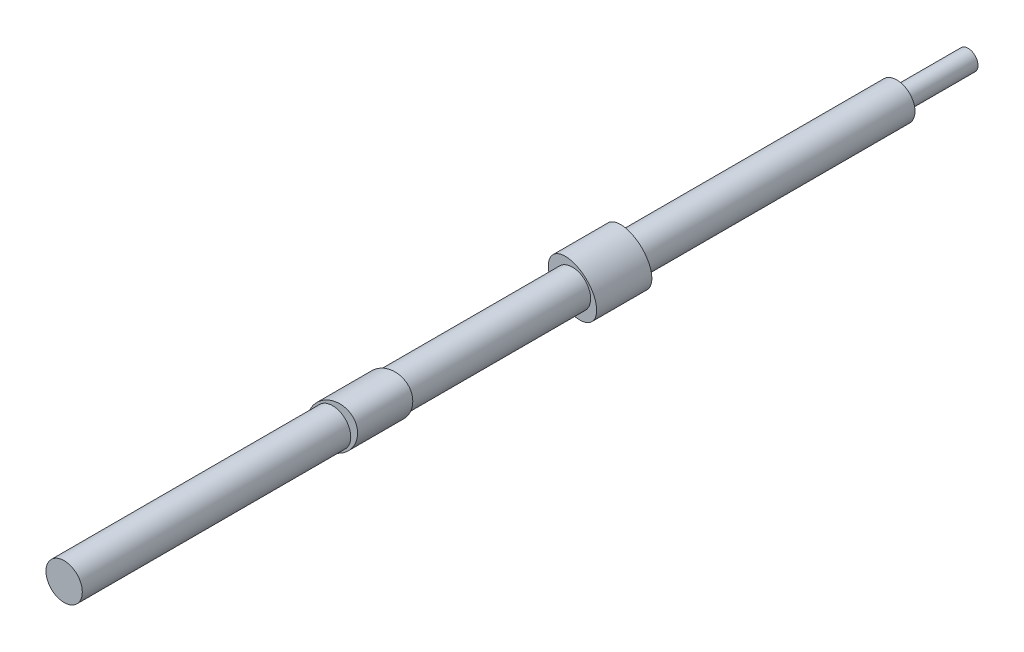
SolidWorks part; units mm, degrees
ref_plane "Ön Düzlem" through (0, 0, 0) normal (0, 0, 1) x (1, 0, 0)
ref_plane "Üst Düzlem" through (0, 0, 0) normal (0, 1, 0) x (1, 0, 0)
ref_plane "Sağ Düzlem" through (0, 0, 0) normal (1, 0, 0) x (0, 0, -1)
sketch "Çizim1" plane through (0, 0, 0) normal (0, 0, 1) x (1, 0, 0)
  circle A0 centre (0, 0) radius 3.9498
extrude "Yükseklik-Ekstrüzyon1" add sketch "Çizim1" along normal mid plane 181
ref_plane "Düzlem1" through (0, 0, 26.1437) normal (0, 0, 1) x (1, 0, 0)
ref_plane "Düzlem2" through (0, 0, -26) normal (0, 0, 1) x (1, 0, 0)
sketch "Çizim2" plane through (0, 0, 26.1437) normal (0, 0, 1) x (1, 0, 0)
  ellipse E0 centre (0, 0) end of major axis (4.6882, 3.7328) minor radius 4.4127
extrude "Yükseklik-Ekstrüzyon2" add sketch "Çizim2" along normal mid plane 12
sketch "Çizim3" plane through (0, 0, -26) normal (0, 0, 1) x (1, 0, 0)
  ellipse E0 centre (0, 0) end of major axis (-4.2597, 4.1653) minor radius 4.3916
extrude "Yükseklik-Ekstrüzyon3" add sketch "Çizim3" along normal mid plane 12
sketch "Çizim4" plane through (0, 0, 90.5) normal (0, 0, 1) x (1, 0, 0)
  circle A0 centre (0, 0) radius 1.0446
sketch "Çizim5" plane through (0, 0, -90.5) normal (0, 0, -1) x (-1, 0, 0)
  circle A0 centre (0, 0) radius 2.1526
extrude "Yükseklik-Ekstrüzyon5" add sketch "Çizim5" along normal mid plane 31
